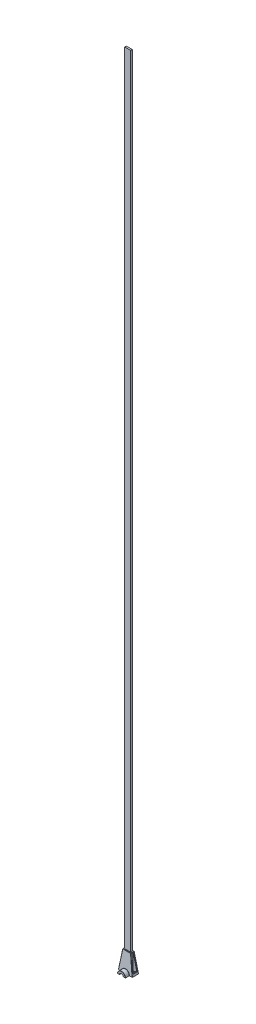
SolidWorks part; units mm, degrees
material "Acier allié inoxydable"
ref_plane "Plan1" through (0, 0, 0) normal (0, 0, 1) x (1, 0, 0)
ref_plane "Plan2" through (0, 0, 0) normal (0, 1, 0) x (1, 0, 0)
ref_plane "Plan3" through (0, 0, 0) normal (1, 0, 0) x (0, 0, -1)
sketch "Esquisse cylindre" plane through (0, 0, 0) normal (0, 0, 1) x (1, 0, 0)
  line L0 (-20, 0) -> (20, 0)
  arc A0 (20, 0) -> (-20, 0) centre (0, 0) ccw
  dimension "D2" = 40
extrude "Cylindre" add sketch "Esquisse cylindre" along normal blind 50
sketch "Esquisse base" plane through (0, 0, 0) normal (0, -1, 0) x (1, 0, 0)
  line L0 (-20, 0) -> (20, 0) construction
  line L1 (35, 30.5) -> (-35, 30.5)
  line L2 (35, 30.5) -> (35, -1.5)
  line L3 (35, -1.5) -> (-35, -1.5)
  line L4 (-35, 30.5) -> (-35, -1.5)
  dimension "D1" = 1.5
  dimension "D2" = 35
  dimension "D3" = 70
  dimension "D4" = 32
ref_plane "Plan extrémité" through (0, 95, 0) normal (0, 1, 0) x (-1, 0, 0)
sketch "Esquisse extrémité" plane through (0, 95, 0) normal (0, 1, 0) x (-1, 0, 0)
  line L0 (-35, -1.5) -> (35, -1.5) construction
  line L1 (-20, 23.5) -> (20, 23.5)
  line L2 (-20, 23.5) -> (-20, 5.5)
  line L3 (-20, 5.5) -> (20, 5.5)
  line L4 (20, 23.5) -> (20, 5.5)
  dimension "D1" = 20
  dimension "D2" = 40
  dimension "D3" = 18
  dimension "D4" = 7
loft "Forme moulée" add profiles "Esquisse base", "Esquisse extrémité"
sketch "Esquisse barre" plane through (0, 95, 0) normal (0, 1, 0) x (-1, 0, 0)
  line L0 (20, 5.5) -> (20, 23.5) construction
  line L1 (-15, 10.5) -> (15, 10.5)
  line L2 (-15, 10.5) -> (-15, 18.5)
  line L3 (-15, 18.5) -> (15, 18.5)
  line L4 (15, 10.5) -> (15, 18.5)
  line L5 (-20, 5.5) -> (20, 5.5) construction
  dimension "D1" = 5
  dimension "D2" = 5
  dimension "D3" = 8
  dimension "D4" = 30
extrude "Barre" add sketch "Esquisse barre" along normal blind 3905
ref_plane "Plan appui écrous" through (0, 12, 0) normal (0, 1, 0) x (-1, 0, 0)
sketch "Esquisse logement" plane through (0, 12, 0) normal (0, 1, 0) x (-1, 0, 0)
  line L1 (-20.2, 18) -> (-20.2, 11)
  line L2 (-35, -1.5) -> (-35, 30.5) construction
  line L3 (-35, 4) -> (-35, 25)
  line L4 (-35, 25) -> (-20.2, 18)
  line L5 (-20.2, 11) -> (-35, 4)
  line L6 (20, 23.5) -> (-20, 23.5) construction
  line L7 (-20, 23.5) -> (-20, 5.5) construction
  dimension "D1" = 5.5
  dimension "D2" = 7
  dimension "D3" = 5.5
  dimension "D4" = 21
  dimension "D5" = 0.2
extrude "Logement" cut sketch "Esquisse logement" along normal up to next
mirror "Symétrie logement" about plane through (0, 0, 0) normal (1, 0, 0)
fillet "Congés R1" radius 1
sketch "Esquisse alésage" plane through (0, 0, 50) normal (0, 0, 1) x (1, 0, 0)
  circle A0 centre (0, 0) radius 10
  dimension "D1" = 20
extrude "Alésage" cut sketch "Esquisse alésage" against normal blind 49
sketch "Esquisse fraisage" plane through (0, 0, 50) normal (0, 0, 1) x (1, 0, 0)
  line L0 (10, 0) -> (19, 0) construction
  line L1 (-36, 1) -> (36, 1)
  line L2 (-36, 1) -> (-36, -1)
  line L3 (-36, -1) -> (36, -1)
  line L4 (36, 1) -> (36, -1)
  dimension "D1" = 72
  dimension "D2" = 1
  dimension "D3" = 2
  dimension "D4" = 36
extrude "Fraisage" cut sketch "Esquisse fraisage" against normal through all
sketch "Esquisse trous" plane through (0, 1, 0) normal (0, -1, 0) x (1, 0, 0)
  line L0 (33.8413, -1.4263) -> (-33.8413, -1.4263) construction
  circle A0 centre (25.5, 14.5737) radius 3.5
  circle A1 centre (-25.5, 14.5737) radius 3.5
  dimension "D1" = 7
  dimension "D2" = 16
  dimension "D3" = 25.5
  dimension "D4" = 51
extrude "Trous" cut sketch "Esquisse trous" against normal through all
sketch "Esquisse rainure" plane through (0, 1, 0) normal (0, -1, 0) x (1, 0, 0)
  line L1 (9.9499, 50) -> (-9.9499, 50) construction
  line L2 (9.9499, 1) -> (-9.9499, 1) construction
  line L3 (3, 42) -> (3, 4)
  line L5 (-3, 42) -> (-3, 4)
  arc A0 (3, 4) -> (-3, 4) centre (0, 4) cw
  arc A1 (3, 42) -> (-3, 42) centre (0, 42) ccw
  dimension "D2" = 8
  dimension "D1" = 6
extrude "Rainure clavette" cut sketch "Esquisse rainure" against normal blind 13.5
ref_plane "Plan4" through (0, 295, 0) normal (0, 1, 0) x (-1, 0, 0)
sketch "Esquisse1" plane through (0, 295, 0) normal (0, 1, 0) x (-1, 0, 0)
  line L0 (-15, 18.5) -> (-15, 10.5) construction
  line L1 (-15, 10.5) -> (15, 10.5) construction
  line L2 (15, 10.5) -> (15, 18.5) construction
  line L3 (15, 18.5) -> (-15, 18.5) construction
  line L4 (-15, 18.5) -> (-15, 10.5)
  line L5 (-15, 10.5) -> (15, 10.5)
  line L6 (15, 10.5) -> (15, 18.5)
  line L7 (15, 18.5) -> (-15, 18.5)
extrude "Enlèv. mat.-Extru.1" [suppressed] cut sketch "Esquisse1" along normal through all
